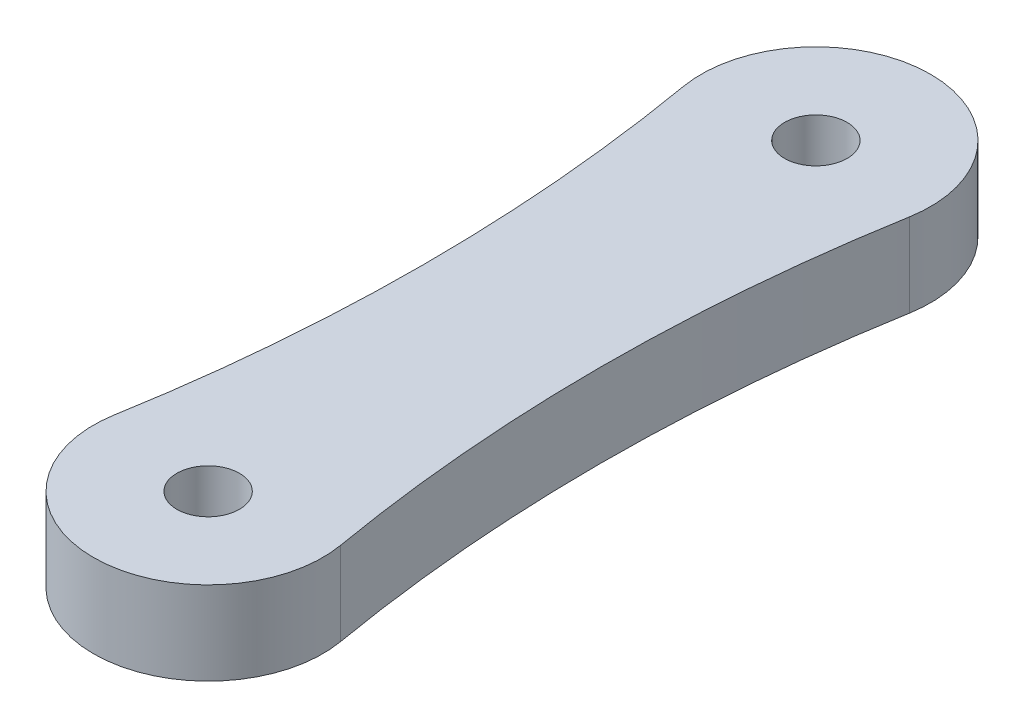
SolidWorks part; units mm, degrees
ref_plane "Front Plane" through (0, 0, 0) normal (0, 0, 1) x (1, 0, 0)
ref_plane "Top Plane" through (0, 0, 0) normal (0, 1, 0) x (1, 0, 0)
ref_plane "Right Plane" through (0, 0, 0) normal (1, 0, 0) x (0, 0, -1)
sketch "Sketch1" plane through (0, 0, 0) normal (0, 1, 0) x (1, 0, 0)
  line L0 (0, 0) -> (0, 29.15) construction
  line L3 (-4.25, 14.575) -> (4.25, 14.575) construction
  circle A2 centre (0, 0) radius 1.5
  circle A3 centre (0, 29.15) radius 1.5
  arc A8 (-5.4197, 0.9365) -> (5.4197, 0.9365) centre (0, 0) ccw
  arc A9 (5.4197, 28.2135) -> (-5.4197, 28.2135) centre (0, 29.15) ccw
  arc A10 (-5.4197, 28.2135) -> (-5.4197, 0.9365) centre (-84.3472, 14.575) cw
  arc A11 (5.4197, 28.2135) -> (5.4197, 0.9365) centre (84.3472, 14.575) ccw
  point P3 (0, 14.575)
  point P16 (-4.25, 14.575)
  point P19 (4.25, 14.575)
  point P23 (0, 14.575)
  dimension "D1" = 3
  dimension "D2" = 29.15
  dimension "D3" = 4
  dimension "D4" = 8.5
extrude "Boss-Extrude1" add sketch "Sketch1" along normal blind 4
